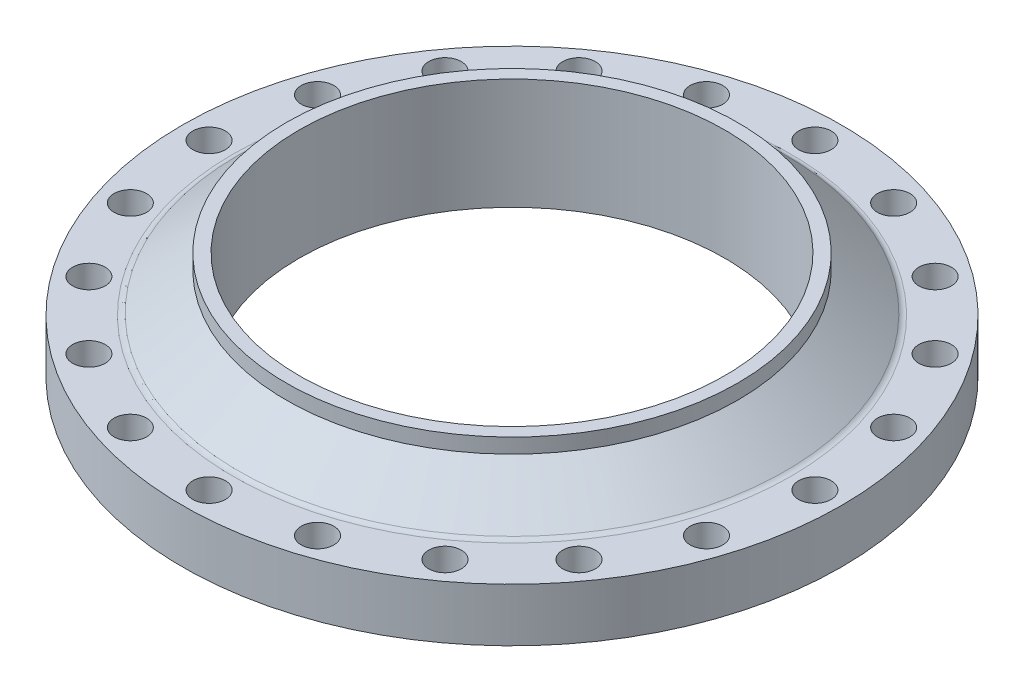
SolidWorks part; units mm, degrees
ref_plane "Front Plane" through (0, 0, 0) normal (0, 0, 1) x (1, 0, 0)
ref_plane "Top Plane" through (0, 0, 0) normal (0, 1, 0) x (1, 0, 0)
ref_plane "Right Plane" through (0, 0, 0) normal (1, 0, 0) x (0, 0, -1)
sketch "Sketch1" plane through (0, 0, 0) normal (0, 0, 1) x (1, 0, 0)
  line L0 (0, 150) -> (0, 0) construction
  line L1 (287.4, 150) -> (304.8, 150)
  line L3 (376.7688, 77) -> (445, 77)
  line L4 (445, 77) -> (445, 5)
  line L5 (445, 5) -> (375, 5)
  line L6 (375, 5) -> (370, 0)
  line L7 (370, 0) -> (287.4, 0)
  line L8 (287.4, 0) -> (287.4, 150)
  line L9 (304.8, 150) -> (304.8, 130)
  line L10 (304.8, 130) -> (369.3809, 79.5439)
  arc A0 (369.3809, 79.5439) -> (376.7688, 77) centre (376.7688, 89) ccw
  dimension "D11" = 12
  dimension "D1" = 150
  dimension "D2" = 287.4
  dimension "D3" = 445
  dimension "D4" = 72
  dimension "D5" = 17.4
  dimension "D6" = 20
  dimension "D7" = 128
  dimension "D8" = 5
  dimension "D9" = 135
  dimension "D10" = 82.6
  dimension "D12" = 142
revolve "Revolve1" add sketch "Sketch1" angle 360 about L0
sketch "Sketch2" plane through (0, 5, 0) normal (0, -1, 0) x (1, 0, 0)
  circle A0 centre (0, 0) radius 409 construction
  circle A1 centre (0, 409) radius 22
  circle A2 centre (126.388, 388.9821) radius 22
  circle A3 centre (240.4042, 330.888) radius 22
  circle A4 centre (330.888, 240.4042) radius 22
  circle A5 centre (388.9821, 126.388) radius 22
  circle A6 centre (409, 0) radius 22
  circle A7 centre (388.9821, -126.388) radius 22
  circle A8 centre (330.888, -240.4042) radius 22
  circle A9 centre (240.4042, -330.888) radius 22
  circle A10 centre (126.388, -388.9821) radius 22
  circle A11 centre (0, -409) radius 22
  circle A12 centre (-126.388, -388.9821) radius 22
  circle A13 centre (-240.4042, -330.888) radius 22
  circle A14 centre (-330.888, -240.4042) radius 22
  circle A15 centre (-388.9821, -126.388) radius 22
  circle A16 centre (-409, 0) radius 22
  circle A17 centre (-388.9821, 126.388) radius 22
  circle A18 centre (-330.888, 240.4042) radius 22
  circle A19 centre (-240.4042, 330.888) radius 22
  circle A20 centre (-126.388, 388.9821) radius 22
  point P46 (0, 0)
  dimension "D1" = 20
extrude "Cut-Extrude2" cut sketch "Sketch2" against normal up to next
